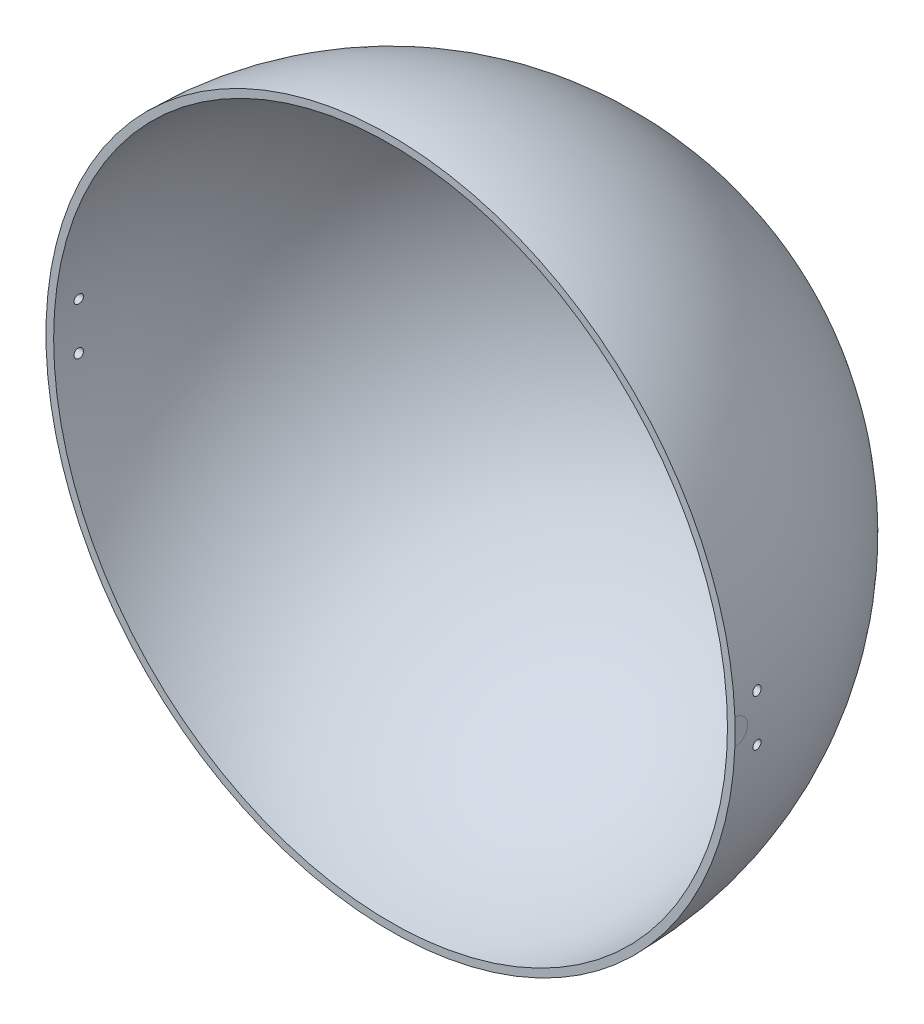
SolidWorks part; units mm, degrees
ref_plane "Спереди" through (0, 0, 0) normal (0, 0, 1) x (1, 0, 0)
ref_plane "Сверху" through (0, 0, 0) normal (0, 1, 0) x (1, 0, 0)
ref_plane "Справа" through (0, 0, 0) normal (1, 0, 0) x (0, 0, -1)
sketch "Эскиз2" plane through (0, 0, 0) normal (0, 1, 0) x (1, 0, 0)
  line L0 (-135, 0) -> (-132, 0)
  line L1 (0, 135) -> (0, 132)
  arc A0 (0, 135) -> (-135, 0) centre (0, 0) ccw
  arc A1 (0, 132) -> (-132, 0) centre (0, 0) ccw
  dimension "D1" = 135
  dimension "D2" = 132
revolve "Повернуть1" add sketch "Эскиз2" angle 360 about L1
sketch "Эскиз3" plane through (0, 0, 0) normal (1, 0, 0) x (0, -1, 0)
  line L0 (-53.4391, -53.4391) -> (42.0203, 42.0203) construction
  line L1 (23.5967, -23.5967) -> (-57.003, 57.003) construction
  circle A1 centre (9.1924, 9.1924) radius 1.75
  circle A2 centre (-9.1924, 9.1924) radius 1.75
  dimension "D2" = 3.5
  dimension "D3" = 3.5
  dimension "D1" = 13
  dimension "D4" = 13
extrude "Вырез-Вытянуть2" cut sketch "Эскиз3" against normal mid plane 423
ref_plane "Плоскость1" through (135, 0, 0) normal (1, 0, 0) x (0, 0, -1)
sketch "Эскиз4" plane through (135, 0, 0) normal (1, 0, 0) x (0, 0, -1)
  circle A0 centre (0, 0) radius 5
  dimension "D1" = 10
extrude "Вырез-Вытянуть3" cut sketch "Эскиз4" against normal blind 0.1
mirror "Зеркальное отражение1" about plane through (0, 0, 0) normal (1, 0, 0) of "Вырез-Вытянуть3"
